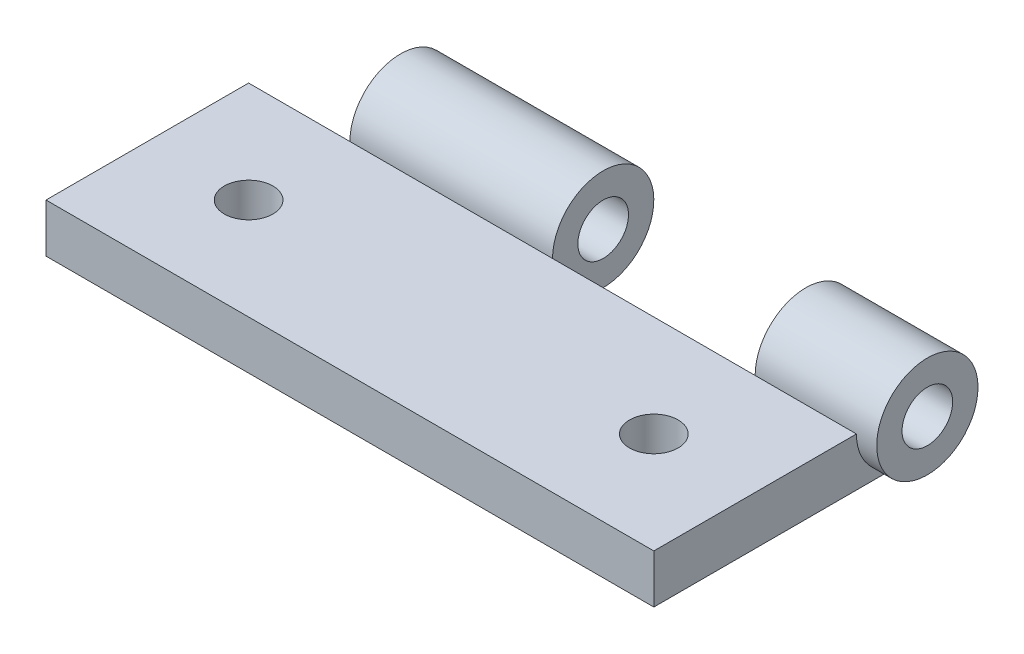
SolidWorks part; units mm, degrees
ref_plane "Front Plane" through (0, 0, 0) normal (0, 0, 1) x (1, 0, 0)
ref_plane "Top Plane" through (0, 0, 0) normal (0, 1, 0) x (1, 0, 0)
ref_plane "Right Plane" through (0, 0, 0) normal (1, 0, 0) x (0, 0, -1)
sketch "Sketch1" plane through (0, 0, 0) normal (0, 1, 0) x (1, 0, 0)
  line L1 (-19.05, -7.9375) -> (19.05, -7.9375)
  line L2 (-19.05, -7.9375) -> (-19.05, 7.9375)
  line L3 (-19.05, 7.9375) -> (19.05, 7.9375)
  line L4 (19.05, -7.9375) -> (19.05, 7.9375)
  line L5 (-19.05, -7.9375) -> (19.05, 7.9375) construction
  line L6 (-19.05, 7.9375) -> (19.05, -7.9375) construction
  point P0 (0, 0)
  dimension "D1" = 38.1
  dimension "D2" = 15.875
extrude "Boss-Extrude1" add sketch "Sketch1" along normal blind 3.048
sketch "Sketch2" plane through (19.05, 0, 0) normal (1, 0, 0) x (0, 0, -1)
  line L0 (6.35, 3.175) -> (12.7534, 3.175) construction
  circle A0 centre (7.9375, 3.048) radius 3.175
  dimension "D1" = 6.35
sketch "Sketch5" plane through (0, 3.048, 0) normal (0, 1, 0) x (1, 0, 0)
  line L0 (19.05, 7.9375) -> (-19.05, 7.9375) construction
  dimension "D1" = 38.1
extrude "Boss-Extrude2" add sketch "Sketch2" along normal blind 1.27 and the other way blind 39.37
sketch "Sketch7" plane through (0, 0, 0) normal (0, 1, 0) x (1, 0, 0)
  line L0 (-12.7, 11.1125) -> (-12.7, 4.7625)
  line L1 (19.05, 4.7625) -> (-19.05, 4.7625) construction
  line L3 (12.7, 11.1125) -> (12.7, 4.7625)
  line L4 (20.32, 11.1125) -> (-20.32, 11.1125) construction
  line L5 (-20.32, 11.1125) -> (-20.32, 4.7625) construction
  dimension "D1" = 6.35
  dimension "D2" = 7.62
  dimension "D3" = 33.02
extrude "Cut-Extrude-Thin2" cut sketch "Sketch7" along normal through all both and the other way through all flip side to cut thin
sketch "Sketch8" plane through (20.32, 0, 0) normal (1, 0, 0) x (0, 0, -1)
  circle A0 centre (7.9375, 3.048) radius 1.5875
  dimension "D1" = 3.175
extrude "Cut-Extrude2" cut sketch "Sketch8" against normal through all
sketch "Sketch9" plane through (0, 3.048, 0) normal (0, 1, 0) x (1, 0, 0)
  line L1 (-19.05, 4.7625) -> (-19.05, -7.9375) construction
  line L3 (19.05, 7.0485) -> (12.7, 7.0485) construction
  circle A0 centre (-12.7, -1.5875) radius 1.524
  circle A1 centre (12.7, -1.5875) radius 1.524
  dimension "D1" = 3.048
  dimension "D2" = 3.048
  dimension "D3" = 8.636
  dimension "D4" = 6.35
  dimension "D5" = 31.75
extrude "Cut-Extrude3" cut sketch "Sketch9" against normal through all
